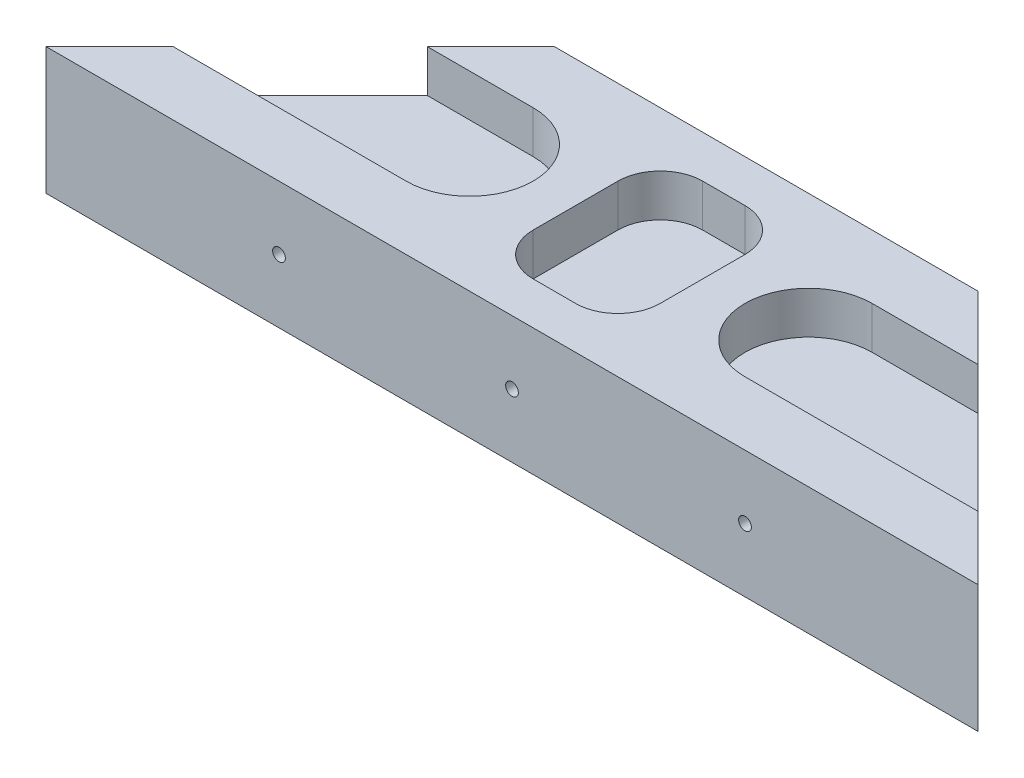
SolidWorks part; units mm, degrees
ref_plane "Front Plane" through (0, 0, 0) normal (0, 0, 1) x (1, 0, 0)
ref_plane "Top Plane" through (0, 0, 0) normal (0, 1, 0) x (1, 0, 0)
ref_plane "Right Plane" through (0, 0, 0) normal (1, 0, 0) x (0, 0, -1)
sketch "Sketch1" plane through (0, 0, 0) normal (0, 1, 0) x (1, 0, 0)
  line L0 (0, 0) -> (110, 0)
  line L1 (110, 0) -> (80, 30)
  line L2 (80, 30) -> (30, 30)
  line L3 (30, 30) -> (0, 0)
  dimension "D1" = 110
  dimension "D2" = 45
  dimension "D3" = 45
  dimension "D4" = 30
extrude "Boss-Extrude1" add sketch "Sketch1" along normal blind 15
sketch "Sketch2" plane through (0, 15, 0) normal (0, 1, 0) x (1, 0, 0)
  line L0 (-5, 15) -> (35, 15) construction
  line L1 (-5, 22.5) -> (35, 22.5)
  line L2 (-5, 7.5) -> (35, 7.5)
  line L4 (30, 30) -> (0, 0) construction
  line L5 (55, 30) -> (55, 0) construction
  line L6 (80, 30) -> (30, 30) construction
  line L7 (0, 0) -> (110, 0) construction
  line L8 (115, 15) -> (75, 15) construction
  line L9 (115, 22.5) -> (75, 22.5)
  line L10 (115, 7.5) -> (75, 7.5)
  arc A0 (-5, 22.5) -> (-5, 7.5) centre (-5, 15) ccw
  arc A1 (35, 7.5) -> (35, 22.5) centre (35, 15) ccw
  arc A2 (115, 22.5) -> (115, 7.5) centre (115, 15) cw
  arc A3 (75, 7.5) -> (75, 22.5) centre (75, 15) cw
  point P2 (15, 15)
  point P11 (15, 15)
  point P18 (95, 15)
  dimension "D1" = 40
  dimension "D2" = 15
extrude "Cut-Extrude1" cut sketch "Sketch2" against normal blind 5
sketch "Sketch3" plane through (0, 0, 0) normal (0, 0, 1) x (1, 0, 0)
  line L0 (0, 7.5) -> (110, 7.5) construction
  line L1 (0, 15) -> (0, 0) construction
  line L2 (110, 15) -> (110, 0) construction
  circle A0 centre (27.5, 7.5) radius 0.75
  circle A1 centre (55, 7.5) radius 0.75
  circle A2 centre (82.5, 7.5) radius 0.75
  dimension "D1" = 1.5
  dimension "D2" = 27.5
  dimension "D3" = 27.5
extrude "Cut-Extrude2" cut sketch "Sketch3" against normal up to surface (30 mm away) up to face at (55, 7.5, -30)
sketch "Sketch4" plane through (0, 15, 0) normal (0, 1, 0) x (1, 0, 0)
  line L0 (80, 30) -> (30, 30) construction
  line L1 (52.5, 25) -> (57.5, 25)
  line L2 (47.5, 20) -> (47.5, 10)
  line L3 (52.5, 5) -> (57.5, 5)
  line L4 (62.5, 20) -> (62.5, 10)
  line L5 (0, 0) -> (110, 0) construction
  arc A0 (35, 7.5) -> (35, 22.5) centre (35, 15) ccw construction
  arc A1 (75, 22.5) -> (75, 7.5) centre (75, 15) ccw construction
  arc A2 (47.5, 10) -> (52.5, 5) centre (52.5, 10) ccw
  arc A3 (57.5, 5) -> (62.5, 10) centre (57.5, 10) ccw
  arc A4 (57.5, 25) -> (62.5, 20) centre (57.5, 20) cw
  arc A5 (52.5, 25) -> (47.5, 20) centre (52.5, 20) ccw
  point P4 (42.5, 15)
  point P5 (67.5, 15)
  dimension "D5" = 5
  dimension "D1" = 5
  dimension "D2" = 5
  dimension "D3" = 5
  dimension "D4" = 5
extrude "Cut-Extrude3" cut sketch "Sketch4" against normal blind 5
